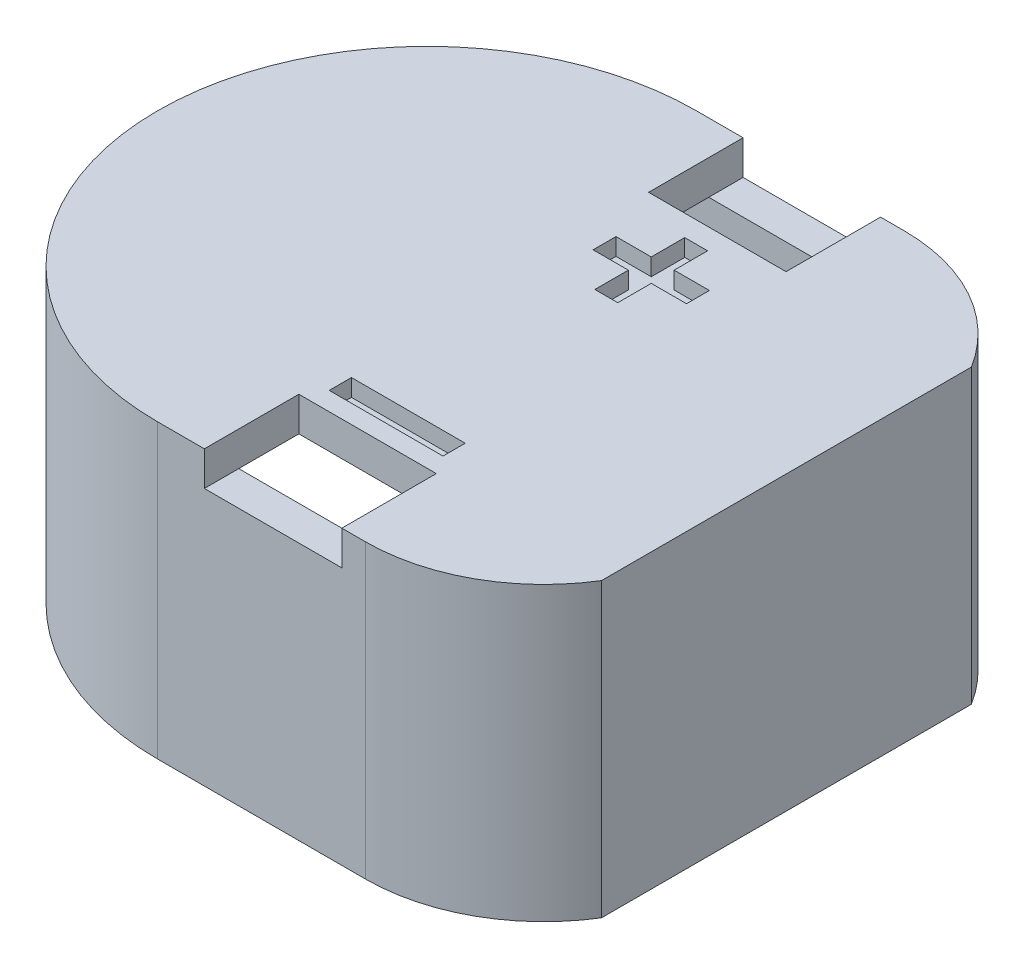
SolidWorks part; units mm, degrees
ref_plane "Front Plane" through (0, 0, 0) normal (0, 0, 1) x (1, 0, 0)
ref_plane "Top Plane" through (0, 0, 0) normal (0, 1, 0) x (1, 0, 0)
ref_plane "Right Plane" through (0, 0, 0) normal (1, 0, 0) x (0, 0, -1)
sketch "Sketch1" plane through (0, 0, 0) normal (0, 1, 0) x (1, 0, 0)
  line L0 (28.0355, 63.0799) -> (140.1777, 63.0799) construction
  line L1 (114.3527, 52.5526) -> (114.3527, 72.5526) construction
  line L2 (95.9295, 75.7305) -> (108.0276, 75.7305) construction
  line L3 (95.9295, 76.2305) -> (108.0276, 76.2305)
  line L4 (95.9295, 49.3747) -> (108.0276, 49.3747) construction
  line L5 (114.8527, 52.3898) -> (114.8527, 72.7153)
  line L6 (95.9295, 48.8747) -> (108.0276, 48.8747)
  line L7 (95.9295, 46.8747) -> (108.0276, 46.8747)
  line L8 (116.8527, 51.7869) -> (116.8527, 73.3182)
  line L9 (95.9295, 78.2305) -> (108.0276, 78.2305)
  arc A0 (95.9295, 75.7305) -> (95.9295, 49.3747) centre (95.9295, 62.5526) ccw construction
  arc A1 (108.0276, 75.7305) -> (114.3527, 72.5526) centre (108.0276, 67.847) cw construction
  arc A2 (108.0276, 49.3747) -> (114.3527, 52.5526) centre (108.0276, 57.2581) ccw construction
  arc A3 (108.0276, 76.2305) -> (114.8527, 72.7153) centre (108.0276, 67.847) cw
  arc A4 (108.0276, 48.8747) -> (114.8527, 52.3898) centre (108.0276, 57.2581) ccw
  arc A5 (95.9295, 76.2305) -> (95.9295, 48.8747) centre (95.9295, 62.5526) ccw
  arc A6 (95.9295, 78.2305) -> (95.9295, 46.8747) centre (95.9295, 62.5526) ccw
  arc A7 (108.0276, 46.8747) -> (116.8527, 51.7869) centre (108.0276, 57.2581) ccw
  arc A8 (108.0276, 78.2305) -> (116.8527, 73.3182) centre (108.0276, 67.847) cw
  point P9 (114.3527, 62.5526)
  dimension "D1" = 20
  dimension "D2" = 0.5
  dimension "D3" = 2.5
extrude "Boss-Extrude1" add sketch "Sketch1" along normal blind 15
sketch "Sketch3" plane through (0, 15, 0) normal (0, 1, 0) x (1, 0, 0)
  line L1 (106.6527, 78.2305) -> (98.6527, 78.2305)
  line L2 (106.6527, 78.2305) -> (106.6527, 72.7305)
  line L3 (95.9295, 46.8747) -> (108.0276, 46.8747)
  line L4 (116.8527, 51.7869) -> (116.8527, 73.3182)
  line L5 (108.0276, 78.2305) -> (95.9295, 78.2305)
  line L6 (95.9295, 46.8747) -> (108.0276, 46.8747)
  line L7 (116.8527, 51.7869) -> (116.8527, 73.3182)
  line L8 (108.0276, 78.2305) -> (95.9295, 78.2305)
  line L9 (106.6527, 72.7305) -> (98.6527, 72.7305)
  line L10 (98.6527, 78.2305) -> (98.6527, 72.7305)
  line L11 (102.6527, 72.7305) -> (102.6527, 78.2305) construction
  line L12 (106.6527, 75.4805) -> (98.6527, 75.4805) construction
  line L13 (95.9295, 62.5526) -> (114.8527, 62.5526) construction
  line L14 (114.8527, 52.3898) -> (114.8527, 72.7153) construction
  line L15 (106.6527, 46.8747) -> (98.6527, 46.8747)
  line L16 (98.6527, 46.8747) -> (98.6527, 52.3747)
  line L17 (106.6527, 46.8747) -> (106.6527, 52.3747)
  line L18 (106.6527, 52.3747) -> (98.6527, 52.3747)
  arc A3 (95.9295, 78.2305) -> (95.9295, 46.8747) centre (95.9295, 62.5526) ccw
  arc A4 (108.0276, 46.8747) -> (116.8527, 51.7869) centre (108.0276, 57.2581) ccw
  arc A5 (116.8527, 73.3182) -> (108.0276, 78.2305) centre (108.0276, 67.847) ccw
  arc A6 (95.9295, 78.2305) -> (95.9295, 46.8747) centre (95.9295, 62.5526) ccw
  arc A7 (108.0276, 46.8747) -> (116.8527, 51.7869) centre (108.0276, 57.2581) ccw
  arc A8 (116.8527, 73.3182) -> (108.0276, 78.2305) centre (108.0276, 67.847) ccw
  point P193 (102.6527, 75.4805)
  arc M12 (95.9295, 78.2305) -> (95.9295, 46.8747) centre (95.9295, 62.5526) ccw
  line M13 (95.9295, 46.8747) -> (108.0276, 46.8747)
  arc M14 (108.0276, 46.8747) -> (116.8527, 51.7869) centre (108.0276, 57.2581) ccw
  line M15 (116.8527, 51.7869) -> (116.8527, 73.3182)
  arc M16 (116.8527, 73.3182) -> (108.0276, 78.2305) centre (108.0276, 67.847) ccw
  line M17 (108.0276, 78.2305) -> (95.9295, 78.2305)
  line M18 (108.0276, 48.8747) -> (95.9295, 48.8747)
  arc M19 (95.9295, 48.8747) -> (95.9295, 76.2305) centre (95.9295, 62.5526) cw
  line M20 (95.9295, 76.2305) -> (108.0276, 76.2305)
  arc M21 (108.0276, 76.2305) -> (114.8527, 72.7153) centre (108.0276, 67.847) cw
  line M22 (114.8527, 72.7153) -> (114.8527, 52.3898)
  arc M23 (114.8527, 52.3898) -> (108.0276, 48.8747) centre (108.0276, 57.2581) cw
  dimension "D2" = 10.2
  dimension "D3" = 8
  dimension "D4" = 5.5
  dimension "D1" = 0
extrude "Boss-Extrude2" add sketch "Sketch3" along normal blind 2 contours L18 L17 L2 L9 L10 L16 M18 M23 M22 M21 M20 M19 | L16 L10 M13 M18 M19 M20 M17 M12 | L17 L2 M13 M14 M15 M16 M17 M20 M21 M22 M23 M18
fillet "Fillet1" [suppressed] radius 2
sketch "Sketch4" plane through (0, 17, 0) normal (0, 1, 0) x (1, 0, 0)
  line L0 (106.6527, 52.3747) -> (98.6527, 52.3747) construction
  line L1 (99.3426, 54.7465) -> (105.9628, 54.7465)
  line L2 (99.3426, 54.7465) -> (99.3426, 53.4522)
  line L3 (99.3426, 53.4522) -> (105.9628, 53.4522)
  line L4 (105.9628, 54.7465) -> (105.9628, 53.4522)
  line L5 (102.6527, 53.4522) -> (102.6527, 54.7465) construction
  line L6 (99.3426, 54.0994) -> (105.9628, 54.0994) construction
  text T0 "+" font "Century Gothic" height 8
  point P5 (102.707, 53.4067)
  point P8 (102.6527, 52.3747)
  point P9 (102.6527, 53.9444)
  point P257 (102.6527, 54.0994)
extrude "Cut-Extrude1" cut sketch "Sketch4" against normal blind 1
